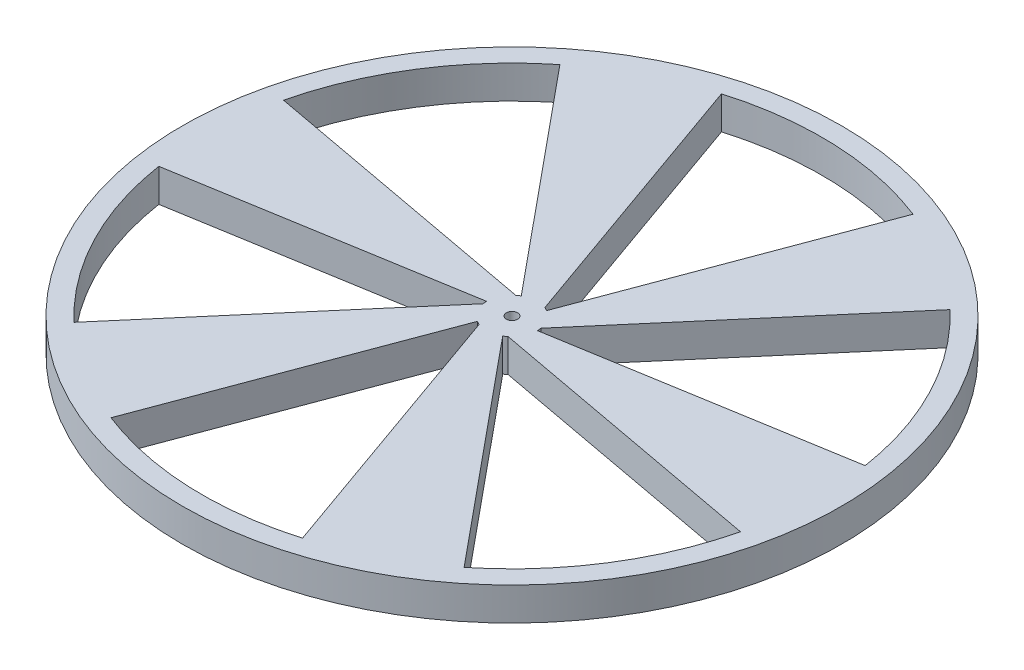
SolidWorks part; units mm, degrees
ref_plane "Front Plane" through (0, 0, 0) normal (0, 0, 1) x (1, 0, 0)
ref_plane "Top Plane" through (0, 0, 0) normal (0, 1, 0) x (1, 0, 0)
ref_plane "Right Plane" through (0, 0, 0) normal (1, 0, 0) x (0, 0, -1)
sketch "Sketch1" plane through (0, 0, 0) normal (0, 1, 0) x (1, 0, 0)
  line L0 (-2.413, 3) -> (-45.6895, 11.0215)
  line L1 (-3.85, 0) -> (-46.4562, -7.1292)
  line L2 (-1.925, 3.3342) -> (-29.4021, 36.6676)
  line L3 (1.3916, 3.5897) -> (-13.2999, 45.079)
  line L4 (1.925, 3.3342) -> (17.054, 43.7968)
  line L5 (3.8046, 0.5897) -> (32.3896, 34.0575)
  line L6 (3.85, 0) -> (46.4562, 7.1292)
  line L7 (2.413, -3) -> (45.6895, -11.0215)
  line L8 (1.925, -3.3342) -> (29.4021, -36.6676)
  line L9 (-1.3916, -3.5897) -> (13.2999, -45.079)
  line L10 (-1.925, -3.3342) -> (-17.054, -43.7968)
  line L11 (-3.8046, -0.5897) -> (-32.3896, -34.0575)
  circle A0 centre (0, 0) radius 50
  circle A1 centre (0, 0) radius 0.85
  circle A2 centre (0, 0) radius 47
  circle A3 centre (0, 0) radius 3.85
  point P8 (-3.85, 0)
  point P33 (0, 0)
  dimension "D1" = 3
  dimension "D2" = 100
  dimension "D3" = 1.7
  dimension "D4" = 3
  dimension "D5" = 3
  dimension "D6" = 20
  dimension "D7" = 6
extrude "Boss-Extrude1" add sketch "Sketch1" along normal blind 5 contours A0 A2 | A3 A1 | A3 L9 A2 L8 | A3 L7 A2 L6 | A3 L5 A2 L4 | A3 L3 A2 L2 | A3 L0 A2 L1 | A3 L11 A2 L10
